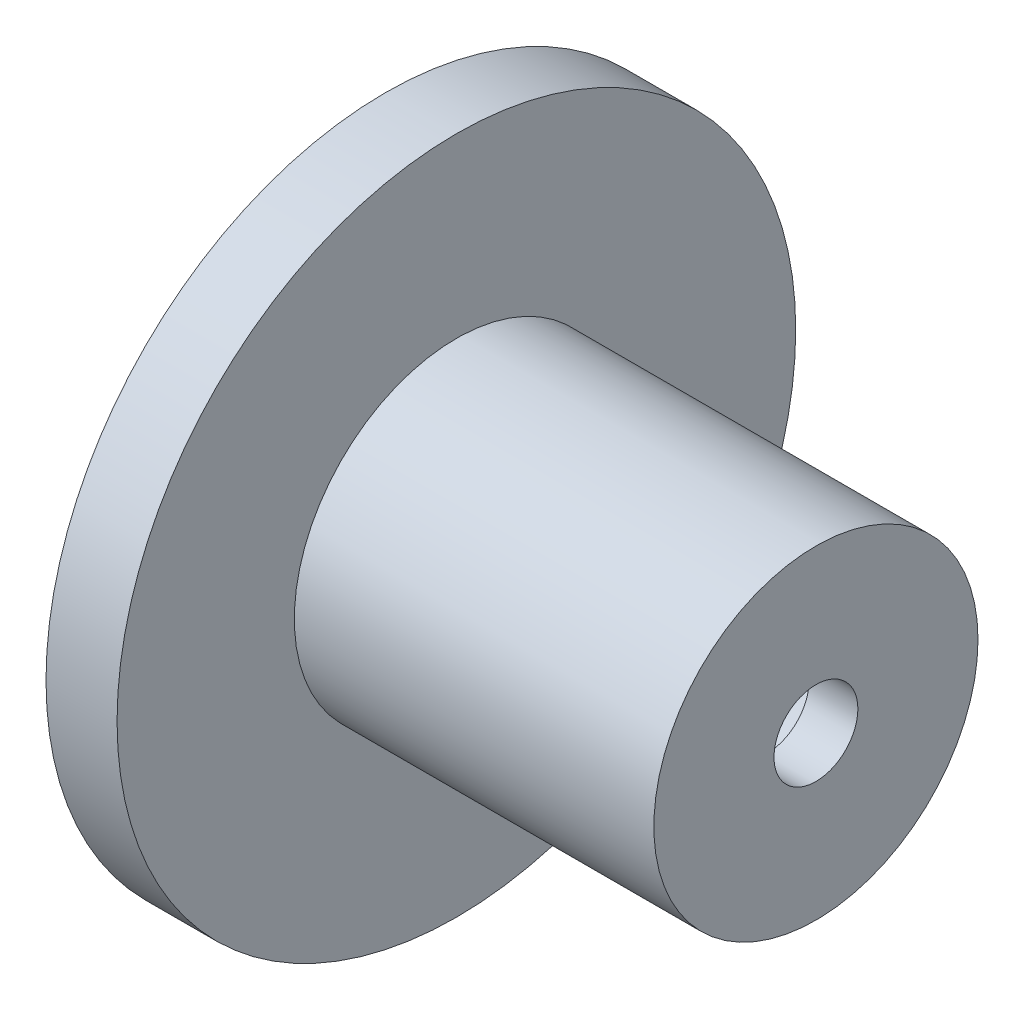
SolidWorks part; units mm, degrees
ref_plane "Front Plane" through (0, 0, 0) normal (0, 0, 1) x (1, 0, 0)
ref_plane "Top Plane" through (0, 0, 0) normal (0, 1, 0) x (1, 0, 0)
ref_plane "Right Plane" through (0, 0, 0) normal (1, 0, 0) x (0, 0, -1)
sketch "Sketch1" plane through (0, 0, 0) normal (0, 0, 1) x (1, 0, 0)
  line L0 (38.6706, 0) -> (36.2373, 0)
  line L1 (36.2373, -6.0938) -> (36.2373, 1.9062) construction
  line L2 (36.2373, 0) -> (36.2373, 3.4743)
  line L3 (36.2373, 3.4743) -> (13.4089, 3.4062)
  line L4 (23.2373, 3.4062) -> (-20.2627, 3.4062) construction
  line L5 (13.4089, 3.4062) -> (13.4089, 5.9946)
  line L6 (13.4089, 5.9946) -> (17.1822, 5.9946)
  line L7 (38.6706, 5.9946) -> (38.6706, 0)
  line L8 (34.2373, -2.0938) -> (-16.7627, -2.0938) construction
  line L9 (34.2373, -5.0938) -> (34.2373, 0.9062) construction
  line L10 (-16.7627, -2.5938) -> (-16.7627, -1.5938) construction
  line L11 (17.1822, 5.9946) -> (17.1822, 14.8409)
  line L12 (17.1822, 14.8409) -> (20.7281, 14.8409)
  line L13 (20.7281, 14.8409) -> (20.7281, 5.9946)
  line L14 (20.7281, 5.9946) -> (38.6706, 5.9946)
revolve "Revolve1" add sketch "Sketch1" angle 360 about L8
